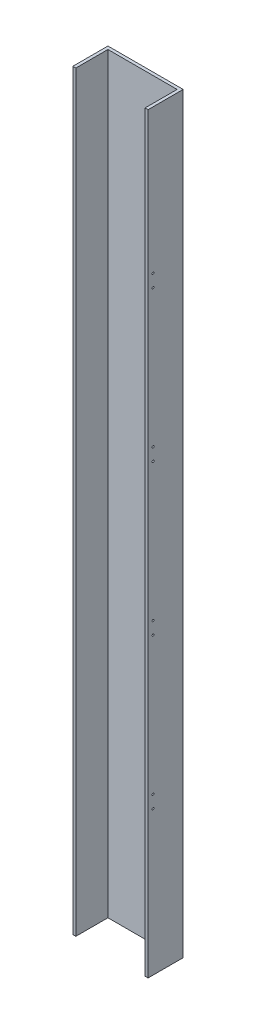
SolidWorks part; units mm, degrees
ref_plane "Front Plane" through (0, 0, 0) normal (0, 0, 1) x (1, 0, 0)
ref_plane "Top Plane" through (0, 0, 0) normal (0, 1, 0) x (1, 0, 0)
ref_plane "Right Plane" through (0, 0, 0) normal (1, 0, 0) x (0, 0, -1)
sketch "Sketch1" plane through (0, 0, 0) normal (0, 1, 0) x (1, 0, 0)
  line L2 (-75, 35) -> (-75, -35)
  line L3 (-75, -35) -> (-69, -35)
  line L4 (-69, -35) -> (-69, 29)
  line L5 (-69, 29) -> (69, 29)
  line L6 (69, 29) -> (69, -35)
  line L7 (69, -35) -> (75, -35)
  line L8 (75, -35) -> (75, 35)
  line L9 (75, 35) -> (-75, 35)
  dimension "D1" = 70
  dimension "D2" = 150
  dimension "D3" = 6
  dimension "D4" = 138
extrude "Boss-Extrude1" add sketch "Sketch1" along normal blind 1500
sketch "Sketch2" plane through (75, 0, 0) normal (1, 0, 0) x (0, 0, -1)
  line L0 (-35, 1500) -> (-35, 0) construction
  line L3 (-35, 0) -> (35, 0) construction
  circle A4 centre (-25, 312.5) radius 2
  circle A5 centre (-25, 287.5) radius 2
  circle A6 centre (-25, 587.5) radius 2
  circle A7 centre (-25, 612.5) radius 2
  circle A8 centre (-25, 1212.5) radius 2
  circle A9 centre (-25, 1187.5) radius 2
  circle A10 centre (-25, 887.5) radius 2
  circle A11 centre (-25, 912.5) radius 2
  dimension "D1" = 4
  dimension "D2" = 10
  dimension "D3" = 287.5
extrude "Cut-Extrude1" cut sketch "Sketch2" against normal blind 6
sketch "Sketch3" plane through (0, 0, -35) normal (0, 0, -1) x (-1, 0, 0)
  line L0 (-75, 1500) -> (-75, 0) construction
  circle A0 centre (-26.75, 75) radius 2.5
  circle A1 centre (-26.75, 225) radius 2.5
  circle A2 centre (-26.75, 375) radius 2.5
  circle A3 centre (-26.75, 525) radius 2.5
  circle A4 centre (-26.75, 675) radius 2.5
  circle A5 centre (-26.75, 825) radius 2.5
  circle A6 centre (-26.75, 975) radius 2.5
  circle A7 centre (-26.75, 1125) radius 2.5
  circle A8 centre (-26.75, 1275) radius 2.5
  circle A9 centre (-26.75, 1425) radius 2.5
  dimension "D1" = 10
  dimension "D2" = 48.25
extrude "Cut-Extrude2" cut sketch "Sketch3" against normal blind 6
